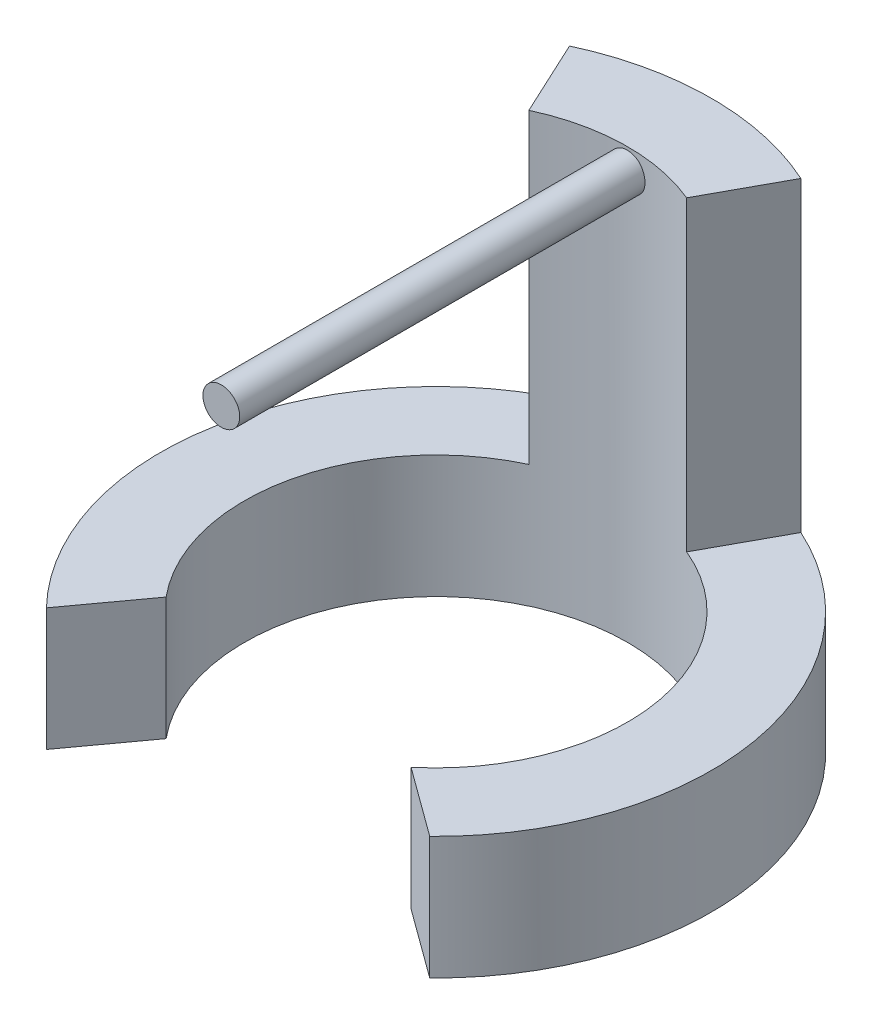
SolidWorks part; units mm, degrees
ref_plane "Front Plane" through (0, 0, 0) normal (0, 0, 1) x (1, 0, 0)
ref_plane "Top Plane" through (0, 0, 0) normal (0, 1, 0) x (1, 0, 0)
ref_plane "Right Plane" through (0, 0, 0) normal (1, 0, 0) x (0, 0, -1)
sketch "Sketch1" plane through (0, 0, 0) normal (0, 1, 0) x (1, 0, 0)
  line L0 (-16.3926, -15.875) -> (-12.2109, -10.1444)
  line L1 (10.1444, -12.2109) -> (15.875, -16.3926)
  arc A0 (10.1444, -12.2109) -> (-12.2109, -10.1444) centre (0, 0) ccw
  arc A1 (15.875, -16.3926) -> (-16.3926, -15.875) centre (0, 0) ccw
extrude "Boss-Extrude1" add sketch "Sketch1" along normal blind 10.16
sketch "Sketch5" plane through (0, 10.16, 0) normal (0, 1, 0) x (1, 0, 0)
  line L0 (-9.6287, 20.6886) -> (-6.6985, 14.3926)
  line L1 (9.4508, 20.7705) -> (6.1118, 14.6514)
  arc A0 (15.875, -16.3926) -> (-16.3926, -15.875) centre (0, 0) ccw construction
  arc A1 (10.1444, -12.2109) -> (-12.2109, -10.1444) centre (0, 0) ccw construction
  arc A2 (-9.6287, 20.6886) -> (9.4508, 20.7705) centre (0, 0) cw
  arc A3 (-6.6985, 14.3926) -> (6.1118, 14.6514) centre (0, 0) cw
extrude "Boss-Extrude2" add sketch "Sketch5" along normal blind 25.4
sketch "Sketch10" plane through (0, 0, 0) normal (0, 0, 1) x (1, 0, 0)
  circle A0 centre (0, 33.782) radius 1.524
extrude "Boss-Extrude3" add sketch "Sketch10" along normal blind 17.78 and the other way blind 17.78 separate body
equation "\"0..4in\"=0.1"
